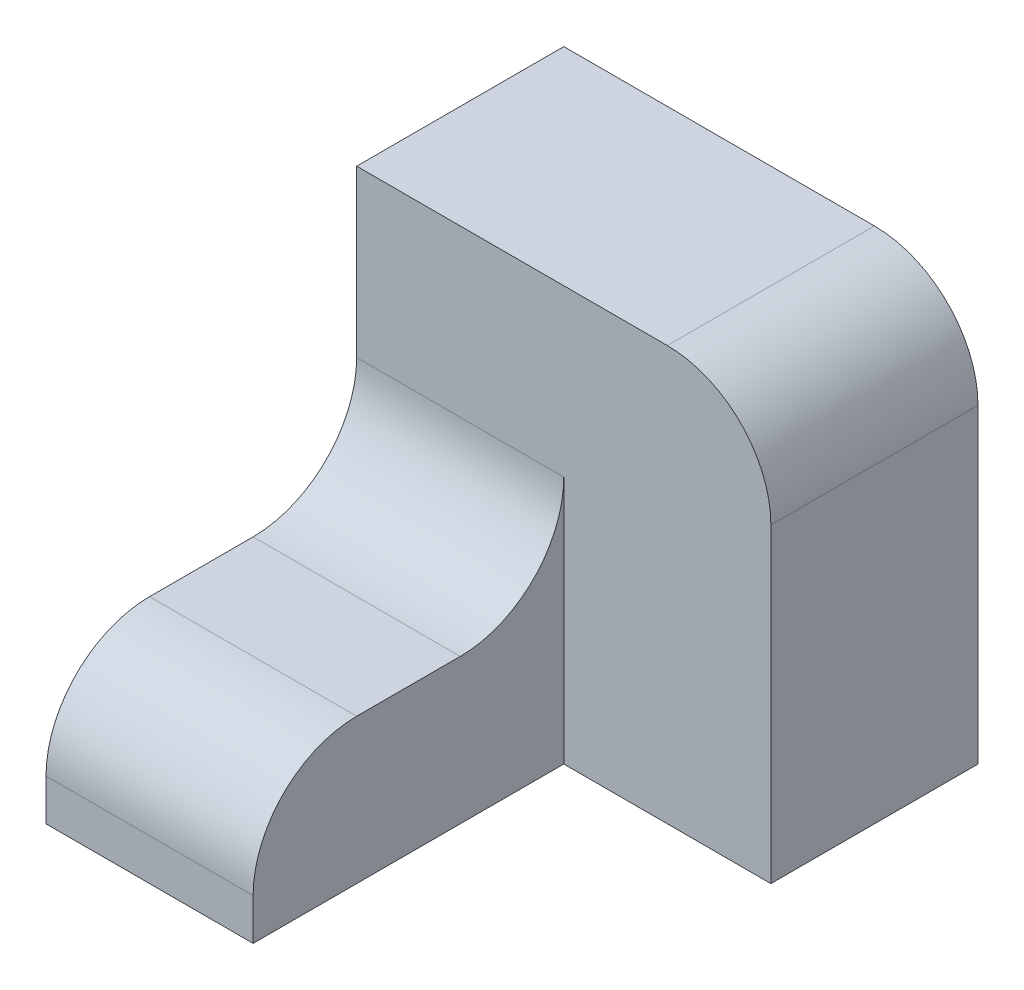
SolidWorks part; units mm, degrees
ref_plane "Front Plane" through (0, 0, 0) normal (0, 0, 1) x (1, 0, 0)
ref_plane "Top Plane" through (0, 0, 0) normal (0, 1, 0) x (1, 0, 0)
ref_plane "Right Plane" through (0, 0, 0) normal (1, 0, 0) x (0, 0, -1)
sketch "Sketch1" plane through (0, 0, 0) normal (0, 0, 1) x (1, 0, 0)
  line L1 (-30, -14) -> (-10, -14)
  line L2 (-10, -14) -> (-10, 0)
  line L3 (-10, 0) -> (-30, 0)
  line L4 (-30, 0) -> (-30, -14)
  dimension "D1" = 20
  dimension "Width" = 14
extrude "Boss-Extrude1" add sketch "Sketch1" along normal blind 30
sketch "Sketch2" plane through (0, 0, 0) normal (0, 0, 1) x (1, 0, 0)
  line L1 (-30, -14) -> (10, -14)
  line L2 (10, -14) -> (10, 26)
  line L3 (10, 26) -> (-30, 26)
  line L4 (-30, 26) -> (-30, -14)
  dimension "D1" = 40
  dimension "Width" = 40
extrude "Boss-Extrude2" add sketch "Sketch2" against normal blind 20
fillet "Fillet1" radius 10 3 edges at (-20, 0, 0) (10, 26, -10) (-20, 0, 30)
